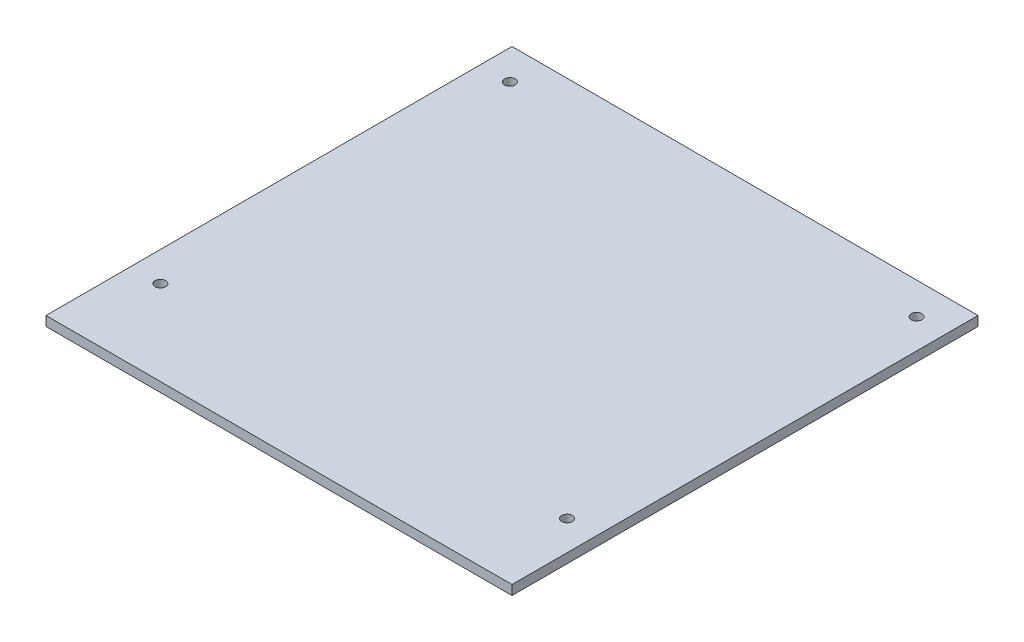
SolidWorks part; units mm, degrees
ref_plane "Front" through (0, 0, 0) normal (0, 0, 1) x (1, 0, 0)
ref_plane "Top" through (0, 0, 0) normal (0, 1, 0) x (1, 0, 0)
ref_plane "Right" through (0, 0, 0) normal (1, 0, 0) x (0, 0, -1)
sketch "Sketch1" plane through (0, 0, 0) normal (0, 1, 0) x (1, 0, 0)
  line L1 (-110, -110) -> (110, -110)
  line L2 (-110, -110) -> (-110, 110)
  line L3 (-110, 110) -> (110, 110)
  line L4 (110, -110) -> (110, 110)
  line L5 (-110, -110) -> (110, 110) construction
  line L6 (-110, 110) -> (110, -110) construction
  point P0 (0, 0)
  dimension "D1" = 220
  dimension "D2" = 220
extrude "Boss-Extrude1" add sketch "Sketch1" along normal blind 4.5
sketch "Sketch2" plane through (0, 4.5, 0) normal (0, 1, 0) x (1, 0, 0)
  circle A0 centre (96, -70) radius 2.5
  circle A1 centre (-96, -70) radius 2.5
  circle A2 centre (-96, 95) radius 2.5
  circle A3 centre (96, 95) radius 2.5
extrude "Cut-Extrude1" cut sketch "Sketch2" against normal through all
